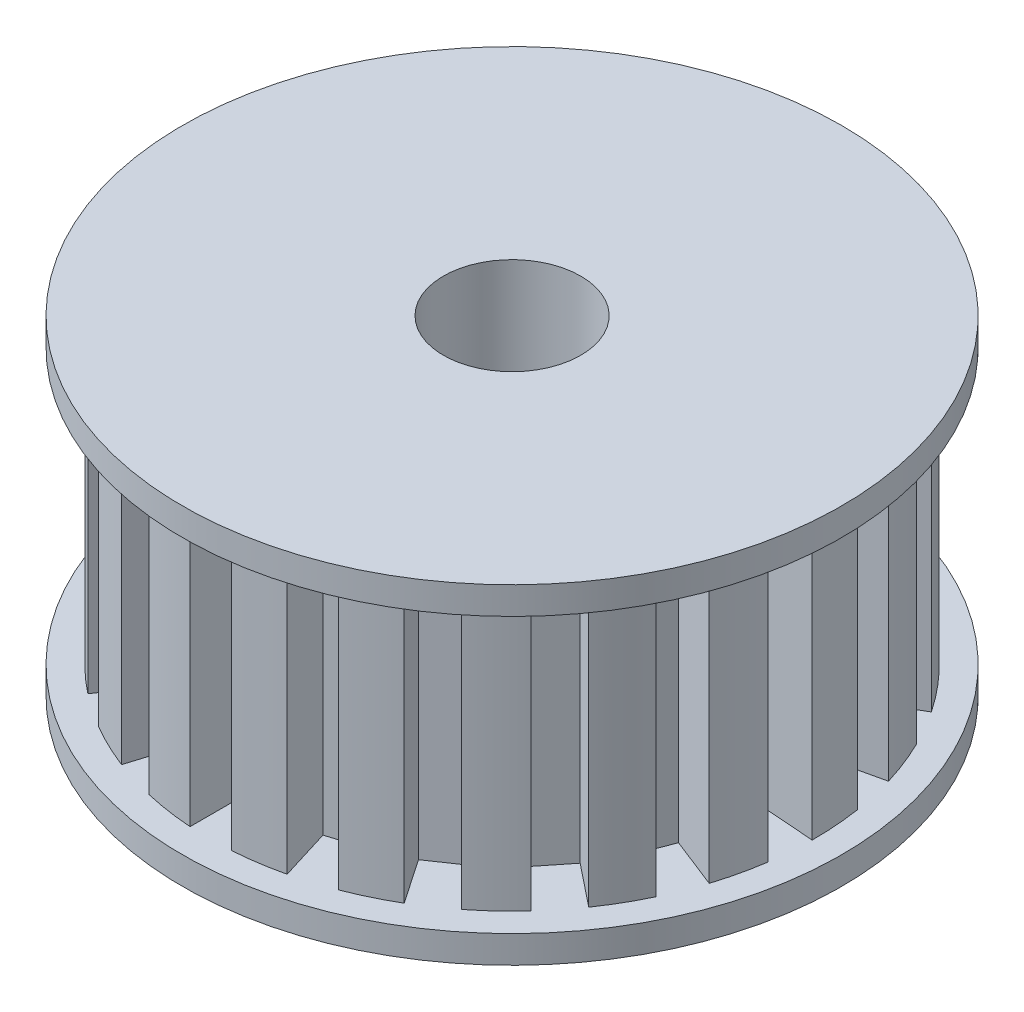
SolidWorks part; units mm, degrees
ref_plane "Front Plane" through (0, 0, 0) normal (0, 0, 1) x (1, 0, 0)
ref_plane "Top Plane" through (0, 0, 0) normal (0, 1, 0) x (1, 0, 0)
ref_plane "Right Plane" through (0, 0, 0) normal (1, 0, 0) x (0, 0, -1)
sketch "Sketch1" plane through (0, 0, 0) normal (0, 0, 1) x (1, 0, 0)
  line L0 (0, 0) -> (0, 6.0691) construction
  line L2 (2.5, -5.9309) -> (4.1776, -5.9309)
  line L3 (2.5, -5.9309) -> (2.5, 6.0691)
  line L4 (2.5, 6.0691) -> (4.1776, 6.0691)
  line L5 (11, -4.9309) -> (11, 5.0691)
  line L6 (4.1776, 6.0691) -> (12, 6.0691)
  line L8 (11, 5.0691) -> (12, 5.0691)
  line L9 (12, 6.0691) -> (12, 5.0691)
  line L10 (4.1776, -5.9309) -> (12, -5.9309)
  line L12 (11, -4.9309) -> (12, -4.9309)
  line L13 (12, -5.9309) -> (12, -4.9309)
  dimension "D1" = 2.5
  dimension "D2" = 9.5
  dimension "D3" = 9.5
  dimension "D4" = 8.5
  dimension "D5" = 10
  dimension "D6" = 12
  dimension "D7" = 1
revolve "Revolve1" add sketch "Sketch1" angle 360 about L0
ref_plane "Plane1" through (0, 0, 11) normal (0, 0, 1) x (1, 0, 0)
sketch "Sketch2" plane through (0, 0, 11) normal (0, 0, 1) x (1, 0, 0)
  line L0 (11, -4.9309) -> (-11, -4.9309) construction
  line L1 (-0.75, 5.0691) -> (0.75, 5.0691)
  line L2 (-0.75, 5.0691) -> (-0.75, -4.9309)
  line L3 (-0.75, -4.9309) -> (0.75, -4.9309)
  line L4 (0.75, 5.0691) -> (0.75, -4.9309)
  line L5 (0, 0) -> (0, -3.0106) construction
  dimension "D1" = 10
  dimension "D2" = 0
  dimension "D3" = 0.75
  dimension "D4" = 1.5
extrude "Cut-Extrude1" cut sketch "Sketch2" against normal blind 2
pattern_circular "CirPattern1" count 21 every 17.143 about axis through (0, 0, 0) along (0, 1, 0) of "Cut-Extrude1"
